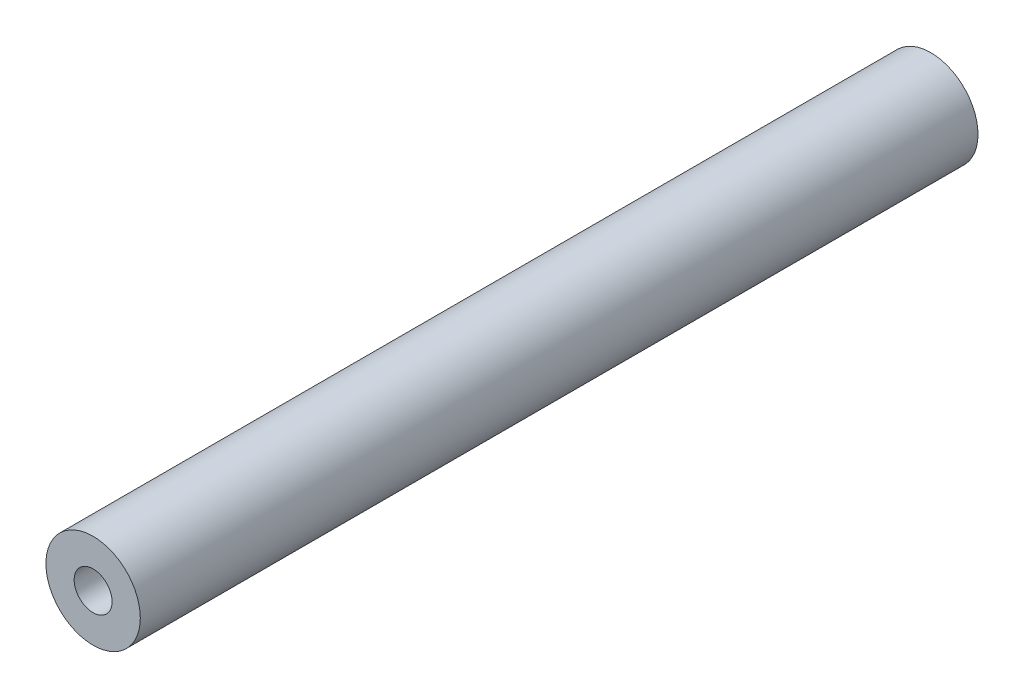
SolidWorks part; units mm, degrees
material "Alum 6061 (Default)"
ref_plane "Front Plane" through (0, 0, 0) normal (0, 0, 1) x (1, 0, 0)
ref_plane "Top Plane" through (0, 0, 0) normal (0, 1, 0) x (1, 0, 0)
ref_plane "Right Plane" through (0, 0, 0) normal (1, 0, 0) x (0, 0, -1)
sketch "Sketch1" plane through (0, 0, 0) normal (0, 0, 1) x (1, 0, 0)
  circle A0 centre (0, 0) radius 6.35
  dimension "Diameter" = 12.7
extrude "Extrude1" add sketch "Sketch1" along normal mid plane 112.7125
hole_wizard "1/4-20 Tapped Hole1" positions "Sketch2" profile "Sketch3" tap size "1/4-20" standard "ANSI Inch"
sketch "Sketch2" plane through (0, 0, 56.3562) normal (0, 0, 1) x (1, 0, 0)
  point P0 (0, 0)
sketch "Sketch3" plane through (0, 0, 56.3562) normal (1, 0, 0) x (0, -1, 0)
  line L0 (0, 0) -> (0, 20.5838)
  line L1 (0, 20.5838) -> (2.5527, 19.05)
  line L2 (2.5527, 19.05) -> (2.5527, 0)
  line L5 (2.5527, 0) -> (0, 0)
  line L10 (0, 20.5838) -> (-2.5527, 19.05) construction
  line L11 (0, -6.35) -> (0, 107.95) construction
  dimension "Tap Drill Dia." = 5.1054
  dimension "Tap Drill Depth" = 19.05
  dimension "Drill Angle" = 118
cosmetic thread "Hole Thread1" parameters "D1"=12.7, "D2"=6.35
hole_wizard "1/4-20 Tapped Hole2" positions "Sketch4" profile "Sketch5" tap size "1/4-20" standard "ANSI Inch"
sketch "Sketch4" plane through (0, 0, -56.3562) normal (0, 0, -1) x (-1, 0, 0)
  point P0 (0, 0)
sketch "Sketch5" plane through (0, 0, -56.3562) normal (1, 0, 0) x (0, 1, 0)
  line L0 (0, 0) -> (0, 20.5838)
  line L1 (0, 20.5838) -> (2.5527, 19.05)
  line L2 (2.5527, 19.05) -> (2.5527, 0)
  line L5 (2.5527, 0) -> (0, 0)
  line L10 (0, 20.5838) -> (-2.5527, 19.05) construction
  line L11 (0, -6.35) -> (0, 107.95) construction
  dimension "Tap Drill Dia." = 5.1054
  dimension "Tap Drill Depth" = 19.05
  dimension "Drill Angle" = 118
cosmetic thread "Hole Thread2" parameters "D1"=12.7, "D2"=6.35
